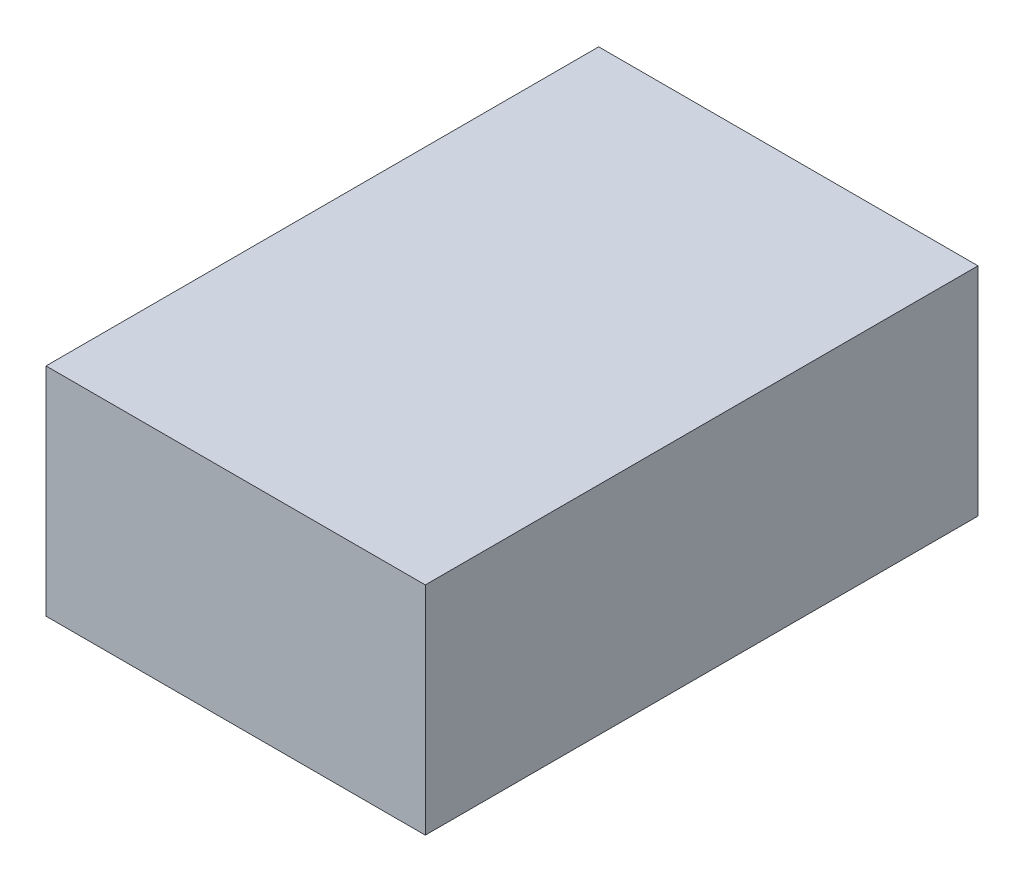
SolidWorks part; units mm, degrees
material "1060-H16"
ref_plane "Front Plane" through (0, 0, 0) normal (0, 0, 1) x (1, 0, 0)
ref_plane "Top Plane" through (0, 0, 0) normal (0, 1, 0) x (1, 0, 0)
ref_plane "Right Plane" through (0, 0, 0) normal (1, 0, 0) x (0, 0, -1)
sketch "Sketch1" plane through (0, 0, 0) normal (0, 1, 0) x (1, 0, 0)
  line L1 (-0.175, 0.255) -> (0.175, 0.255)
  line L2 (-0.175, 0.255) -> (-0.175, -0.255)
  line L3 (-0.175, -0.255) -> (0.175, -0.255)
  line L4 (0.175, 0.255) -> (0.175, -0.255)
  line L5 (-0.175, 0.255) -> (0.175, -0.255) construction
  line L6 (-0.175, -0.255) -> (0.175, 0.255) construction
  point P0 (0, 0)
  dimension "D1" = 0.35
  dimension "D2" = 0.51
extrude "Boss-Extrude1" add sketch "Sketch1" along normal blind 0.2
